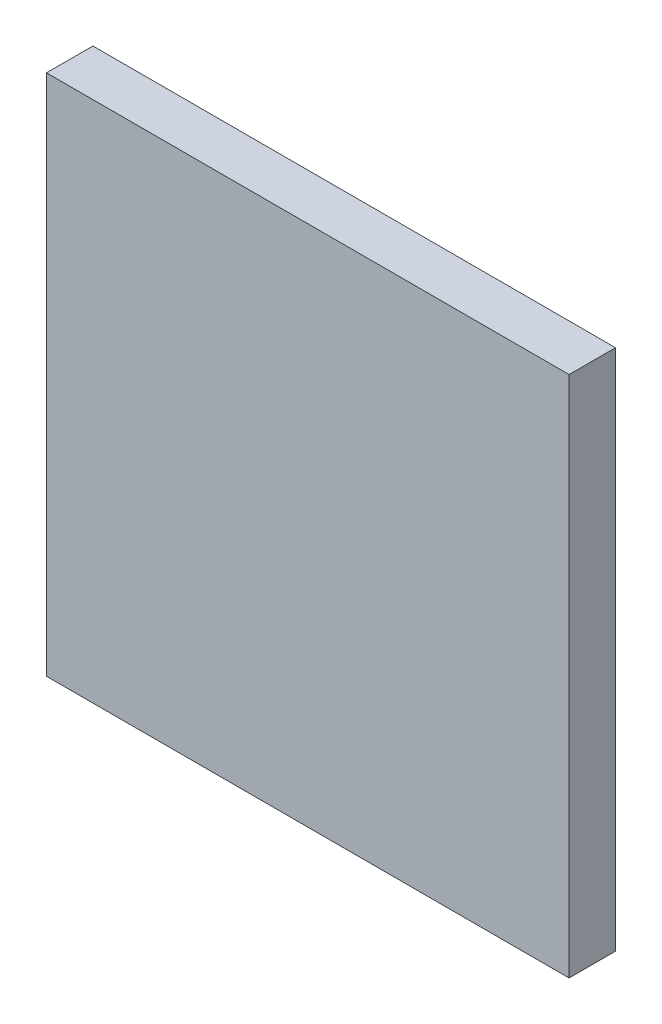
SolidWorks part; units mm, degrees
ref_plane "Front Plane" through (0, 0, 0) normal (0, 0, 1) x (1, 0, 0)
ref_plane "Top Plane" through (0, 0, 0) normal (0, 1, 0) x (1, 0, 0)
ref_plane "Right Plane" through (0, 0, 0) normal (1, 0, 0) x (0, 0, -1)
sketch "Sketch1" plane through (0, 0, 0) normal (0, 0, 1) x (1, 0, 0)
  line L1 (0, 0) -> (45, 0)
  line L2 (0, 0) -> (0, 45)
  line L3 (0, 45) -> (45, 45)
  line L4 (45, 0) -> (45, 45)
  dimension "D1" = 45
  dimension "D2" = 45
extrude "Boss-Extrude1" add sketch "Sketch1" along normal blind 4
